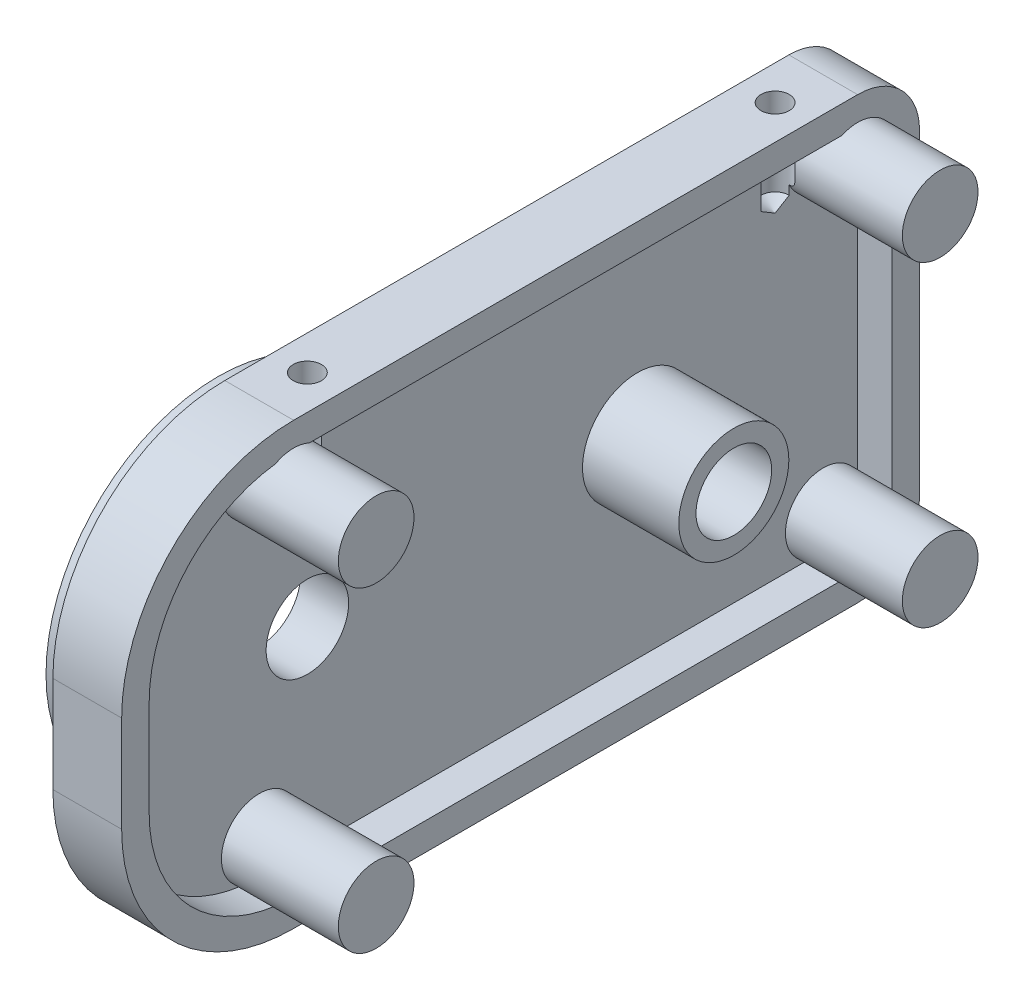
SolidWorks part; units mm, degrees
material "Delrin 2700 NC010, Low Viscosity Acetal Copolymer (SS)"
ref_plane "Front Plane" through (0, 0, 0) normal (0, 0, 1) x (1, 0, 0)
ref_plane "Top Plane" through (0, 0, 0) normal (0, 1, 0) x (1, 0, 0)
ref_plane "Right Plane" through (0, 0, 0) normal (1, 0, 0) x (0, 0, -1)
sketch "Sketch1" plane through (0, 0, 0) normal (1, 0, 0) x (0, 0, -1)
  line L0 (0, 0) -> (29, 0) construction
  line L1 (-29, -16) -> (29, -16)
  line L2 (-29, -16) -> (-29, 16)
  line L3 (-29, 16) -> (29, 16)
  line L4 (29, -16) -> (29, 16)
  line L5 (-29, -16) -> (29, 16) construction
  line L6 (-29, 16) -> (29, -16) construction
  circle A0 centre (11, 0) radius 2.75
  point P0 (0, 0)
  dimension "D3" = 18
  dimension "D4" = 5.5
  dimension "D1" = 32
  dimension "D2" = 58
extrude "Boss-Extrude1" add sketch "Sketch1" along normal blind 5
sketch "Sketch2" plane through (5, 0, 0) normal (1, 0, 0) x (0, 0, -1)
  circle A0 centre (11, 0) radius 4
  circle A1 centre (11, 0) radius 2.75 construction
  circle A2 centre (11, 0) radius 2.75
  dimension "D1" = 8
extrude "Boss-Extrude2" add sketch "Sketch2" along normal blind 4.5
fillet "Fillet1" radius 4.5 2 edges at (2.5, -16, -29) (2.5, 16, -29)
fillet "Fillet2" radius 12.5 2 edges at (2.5, -16, 29) (2.5, 16, 29)
sketch "Sketch4" plane through (5, 0, 0) normal (1, 0, 0) x (0, 0, -1)
  line L1 (24.5, -11.5) -> (-16.5, -11.5)
  line L2 (24.5, -11.5) -> (24.5, 11.5)
  line L3 (24.5, 11.5) -> (-16.5, 11.5)
  line L4 (-16.5, -11.5) -> (-16.5, 11.5)
  circle A0 centre (24.5, 11.5) radius 2.75
  circle A1 centre (24.5, -11.5) radius 2.75
  circle A4 centre (-16.5, 11.5) radius 2.75
  circle A5 centre (-16.5, -11.5) radius 2.75
  dimension "D1" = 5.5
  dimension "D2" = 41
extrude "Boss-Extrude3" add sketch "Sketch4" along normal blind 6 contours A4 | A5 | A1 | A0
sketch "Sketch8" plane through (0, 0, 0) normal (-1, 0, 0) x (0, 0, 1)
  line L0 (29, 0) -> (-29, 0) construction
  line L1 (29, -3.5) -> (29, 3.5) construction
  line L2 (-29, -11.5) -> (-29, 11.5) construction
  circle A0 centre (13, 0) radius 12.5
  circle A1 centre (-11, 0) radius 2.75 construction
  dimension "D1" = 25
  dimension "D2" = 24
extrude "Boss-Extrude4" add sketch "Sketch8" along normal blind 4
sketch "Sketch9" plane through (-4, 0, 0) normal (-1, 0, 0) x (0, 0, 1)
  circle A0 centre (13, 0) radius 10
  dimension "D1" = 20
extrude "Cut-Extrude2" cut sketch "Sketch9" against normal blind 3
sketch "Sketch10" plane through (-1, 0, 0) normal (-1, 0, 0) x (0, 0, 1)
  circle A0 centre (13, 0) radius 3
  dimension "D1" = 6
extrude "Cut-Extrude3" cut sketch "Sketch10" against normal through all
sketch "Sketch3" plane through (5, 0, 0) normal (1, 0, 0) x (0, 0, -1)
  line L8 (-27, 3.5) -> (-27, -3.5)
  line L9 (-16.5, -14) -> (24.5, -14)
  line L10 (27, -11.5) -> (27, 11.5)
  line L11 (24.5, 14) -> (-16.5, 14)
  line L12 (-27, 3.5) -> (-27, -3.5)
  line L13 (-16.5, -14) -> (24.5, -14)
  line L14 (27, -11.5) -> (27, 11.5)
  line L15 (24.5, 14) -> (-16.5, 14)
  circle A4 centre (-16.5, 11.5) radius 2.75 construction
  circle A5 centre (11, 0) radius 4 construction
  circle A6 centre (11, 0) radius 4
  circle A7 centre (-16.5, -11.5) radius 2.75 construction
  arc A8 (-27, -3.5) -> (-16.5, -14) centre (-16.5, -3.5) ccw
  arc A9 (24.5, -14) -> (27, -11.5) centre (24.5, -11.5) ccw
  arc A10 (27, 11.5) -> (24.5, 14) centre (24.5, 11.5) ccw
  arc A11 (-16.5, 14) -> (-27, 3.5) centre (-16.5, 3.5) ccw
  arc A12 (-27, -3.5) -> (-16.5, -14) centre (-16.5, -3.5) ccw
  arc A13 (24.5, -14) -> (27, -11.5) centre (24.5, -11.5) ccw
  arc A14 (27, 11.5) -> (24.5, 14) centre (24.5, 11.5) ccw
  arc A15 (-16.5, 14) -> (-27, 3.5) centre (-16.5, 3.5) ccw
  circle A16 centre (24.5, -11.5) radius 2.75 construction
  circle A17 centre (24.5, 11.5) radius 2.75 construction
  circle A18 centre (-16.5, 11.5) radius 2.75
  circle A19 centre (-16.5, -11.5) radius 2.75
  circle A20 centre (24.5, -11.5) radius 2.75
  circle A21 centre (24.5, 11.5) radius 2.75
  circle M17 centre (11, 0) radius 4
  circle M19 centre (24.5, -11.5) radius 2.75
  circle M20 centre (-16.5, 11.5) radius 2.75
  circle M21 centre (-16.5, -11.5) radius 2.75
  circle M22 centre (24.5, 11.5) radius 2.75
  dimension "D1" = 2
extrude "Cut-Extrude1" cut sketch "Sketch3" against normal blind 2.5 contours L15 A15 L12 A12 L13 L14 M21 M19 M22 M20 M17
hole_wizard "M2.5x0.45 Tapped Hole1" positions "Sketch7" profile "Sketch6" tap size "M2.5x0.45" standard "ANSI Metric"
sketch "Sketch7" plane through (0, 16, 0) normal (0, 1, 0) x (1, 0, 0)
  line L0 (2.5, 29) -> (2.5, -29) construction
  line L1 (0, 29) -> (5, 29) construction
  line L2 (5, -29) -> (0, -29) construction
  line L6 (11, 24.5) -> (11, -16.5) construction
  line L7 (11, 21.75) -> (11, 27.25) construction
  line L8 (11, -19.25) -> (11, -13.75) construction
  line L10 (11, 4) -> (0, 4) construction
  line L11 (0, -16.5) -> (0, 24.5) construction
  point P9 (2.5, 21)
  point P11 (2.5, -13)
  dimension "D1" = 34
  dimension "D2" = 17
sketch "Sketch6" plane through (2.5, 16, -21) normal (1, 0, 0) x (0, 0, 1)
  line L0 (0, 0) -> (0, 6.9659)
  line L1 (0, 6.9659) -> (1.025, 6.35)
  line L2 (1.025, 6.35) -> (1.025, 0)
  line L5 (1.025, 0) -> (0, 0)
  line L10 (0, 6.9659) -> (-1.025, 6.35) construction
  line L11 (0, -6.35) -> (0, 107.95) construction
  dimension "Tap Drill Dia." = 2.05
  dimension "Tap Drill Depth" = 6.35
  dimension "Drill Angle" = 118
cosmetic thread "Hole Thread1" parameters "D1"=5, "D2"=2.5
cosmetic thread "Hole Thread2" parameters "D1"=5, "D2"=2.5
